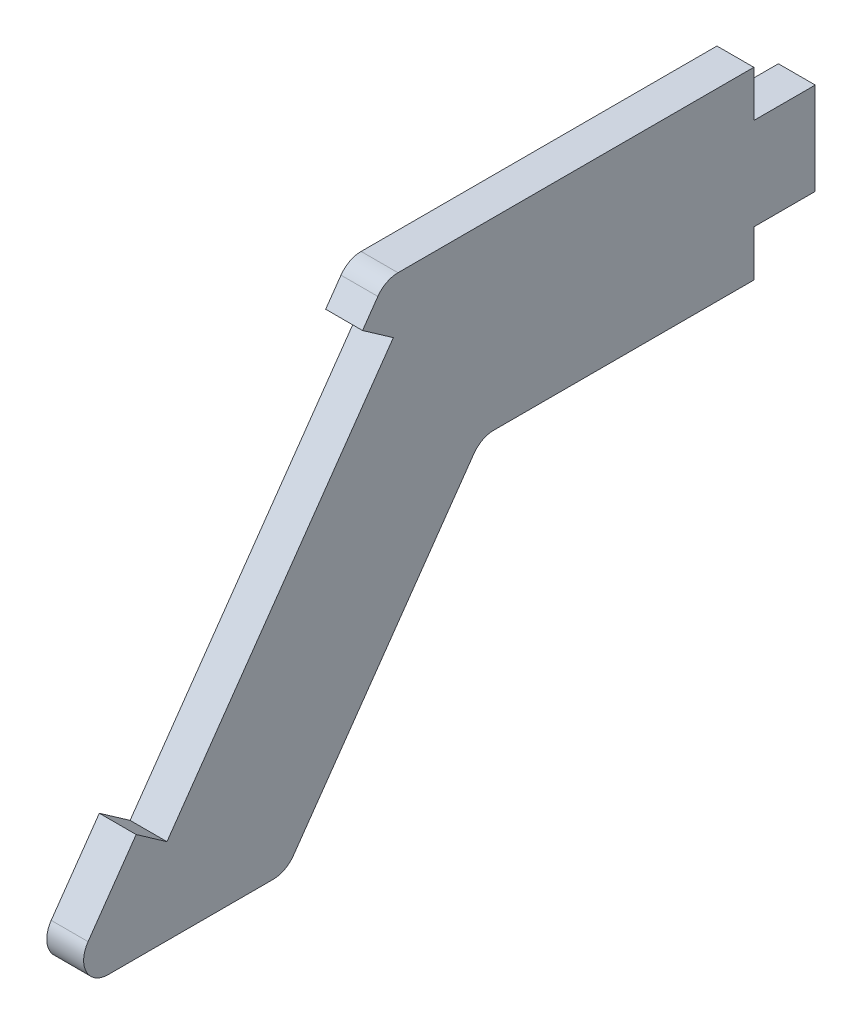
SolidWorks part; units mm, degrees
ref_plane "Front Plane" through (0, 0, 0) normal (0, 0, 1) x (1, 0, 0)
ref_plane "Top Plane" through (0, 0, 0) normal (0, 1, 0) x (1, 0, 0)
ref_plane "Right Plane" through (0, 0, 0) normal (1, 0, 0) x (0, 0, -1)
sketch "Sketch2" plane through (0, 0, 0) normal (1, 0, 0) x (0, 0, -1)
  line L0 (0, -99.6044) -> (-28.9589, -99.6044)
  line L1 (-30.5972, -100.4573) -> (-54.1809, -134.1383)
  line L2 (-52.5426, -137.2854) -> (-39.114, -137.2854)
  line L3 (-37.4757, -136.4326) -> (-22.7887, -115.4573)
  line L4 (-21.1504, -114.6044) -> (0, -114.6044)
  line L5 (0, -99.6044) -> (0, -103.3544)
  line L6 (0, -101.1956) -> (0, -110.25) construction
  line L7 (5, -122.6044) -> (0, -122.6044) construction
  line L8 (5, -110.25) -> (5, -122.6044) construction
  line L9 (0, -103.3544) -> (5, -103.3544)
  line L11 (0, -110.8544) -> (5, -110.8544)
  line L12 (5, -103.3544) -> (5, -110.8544)
  line L13 (0, -107.1044) -> (2.1959, -107.1044) construction
  line L14 (0, -110.8544) -> (0, -114.6044)
  line L15 (5, -101.4729) -> (5, -110.6044) construction
  arc A0 (-28.9589, -99.6044) -> (-30.5972, -100.4573) centre (-28.9589, -101.6044) ccw
  arc A1 (-22.7887, -115.4573) -> (-21.1504, -114.6044) centre (-21.1504, -116.6044) cw
  arc A2 (-39.114, -137.2854) -> (-37.4757, -136.4326) centre (-39.114, -135.2854) ccw
  arc A3 (-54.1809, -134.1383) -> (-52.5426, -137.2854) centre (-52.5426, -135.2854) ccw
  point P16 (-30, -99.6044)
  point P23 (-56.3845, -137.2854)
  dimension "D7" = 2
  dimension "D1" = 15
  dimension "D2" = 15
  dimension "D3" = 30
  dimension "D4" = 46
  dimension "D5" = 125
  dimension "D6" = 8
  dimension "D8" = 7.5
  dimension "D9" = 3.75
  dimension "D10" = 5
extrude "Boss-Extrude1" add sketch "Sketch2" along normal blind 3
sketch "Sketch3" plane through (0, 0, 0) normal (-1, 0, 0) x (0, 0, 1)
  line L0 (50.2662, -128.5475) -> (47.7596, -130.3027)
  line L1 (31.8429, -102.2364) -> (29.3363, -103.9915)
  line L2 (29.3363, -103.9915) -> (31.8429, -102.2364) construction
  line L3 (30.5972, -100.4573) -> (54.1809, -134.1383) construction
  line L4 (31.8429, -102.2364) -> (50.2662, -128.5475)
  line L7 (29.3363, -103.9915) -> (47.7596, -130.3027)
  point P5 (29.2904, -103.926)
  dimension "D1" = 32.12
  dimension "D2" = 3.06
  dimension "D3" = 32.12
  dimension "D4" = 3.06
extrude "Cut-Extrude1" cut sketch "Sketch3" against normal up to surface (3 mm away) up to face at (3, -115.5849, 19.8477)
